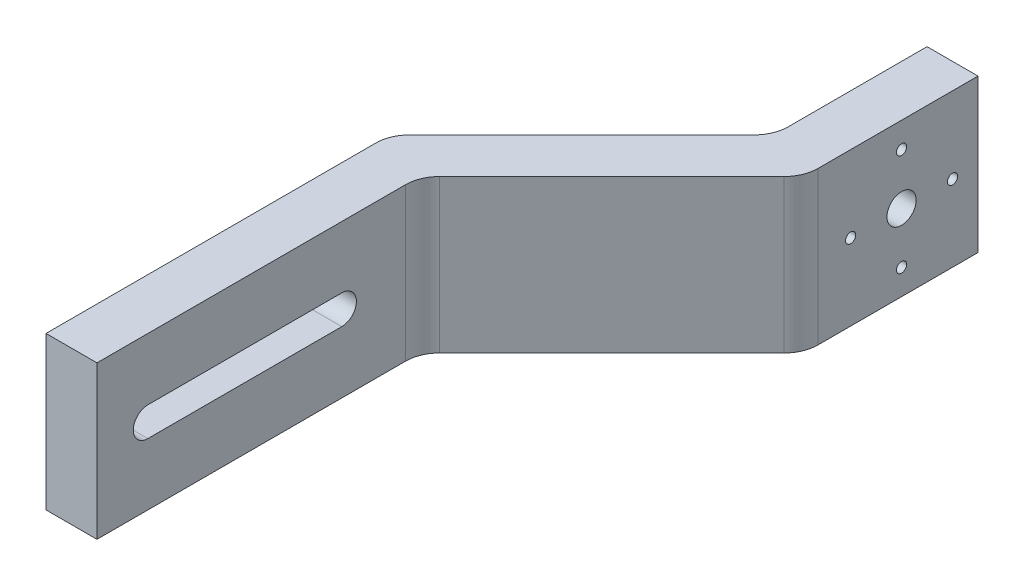
SolidWorks part; units mm, degrees
ref_plane "Front Plane" through (0, 0, 0) normal (0, 0, 1) x (1, 0, 0)
ref_plane "Top Plane" through (0, 0, 0) normal (0, 1, 0) x (1, 0, 0)
ref_plane "Right Plane" through (0, 0, 0) normal (1, 0, 0) x (0, 0, -1)
sketch "Sketch1" plane through (0, 0, 0) normal (0, 1, 0) x (1, 0, 0)
  line L0 (0, 0) -> (0, 101.2132)
  line L1 (0, 101.2132) -> (56.5685, 157.7817)
  line L2 (56.5685, 157.7817) -> (56.5685, 202.7817)
  line L3 (56.5685, 202.7817) -> (71.5685, 202.7817)
  line L4 (71.5685, 202.7817) -> (71.5685, 151.5685)
  line L5 (71.5685, 151.5685) -> (15, 95)
  line L6 (15, 95) -> (15, 0)
  line L7 (15, 0) -> (0, 0)
  dimension "D1" = 15
  dimension "D2" = 15
  dimension "D3" = 15
  dimension "D4" = 80
  dimension "D5" = 45
  dimension "D6" = 95
  dimension "D7" = 135
extrude "Body" add sketch "Sketch1" along normal blind 45
sketch "Sketch3" plane through (56.5685, 0, 0) normal (-1, 0, 0) x (0, 0, 1)
  line L0 (-157.7817, 45) -> (-202.7817, 0) construction
  line L1 (-180.2817, 22.5) -> (-180.2817, 37.5) construction
  circle A0 centre (-180.2817, 22.5) radius 4.3
  circle A1 centre (-180.2817, 22.5) radius 15 construction
  circle A2 centre (-180.2817, 37.5) radius 1.5
  circle A3 centre (-165.2817, 22.5) radius 1.5
  circle A4 centre (-180.2817, 7.5) radius 1.5
  circle A5 centre (-195.2817, 22.5) radius 1.5
  point P9 (-180.2817, 22.5)
  point P10 (-195.2817, 22.5)
  point P18 (-180.2817, 22.5)
  dimension "D1" = 8.6
  dimension "D2" = 30
  dimension "D3" = 3
  dimension "D4" = 4
extrude "Mounting Holes" cut sketch "Sketch3" against normal up to next
sketch "Sketch4" plane through (56.5685, 0, 0) normal (-1, 0, 0) x (0, 0, 1)
  line L0 (-162.4317, 20.8546) -> (-162.4317, 24.1454)
  line L1 (-178.6363, 40.35) -> (-181.9272, 40.35)
  line L2 (-181.9272, 40.35) -> (-183.5726, 37.5)
  line L3 (-183.5726, 37.5) -> (-181.9272, 34.65)
  line L4 (-181.9272, 34.65) -> (-178.6363, 34.65)
  line L5 (-178.6363, 34.65) -> (-176.9908, 37.5)
  line L6 (-176.9908, 37.5) -> (-178.6363, 40.35)
  line L7 (-162.4317, 24.1454) -> (-165.2817, 25.7909)
  line L8 (-165.2817, 25.7909) -> (-168.1317, 24.1454)
  line L9 (-168.1317, 24.1454) -> (-168.1317, 20.8546)
  line L10 (-168.1317, 20.8546) -> (-165.2817, 19.2091)
  line L11 (-165.2817, 19.2091) -> (-162.4317, 20.8546)
  line L12 (-181.9272, 4.65) -> (-178.6363, 4.65)
  line L13 (-178.6363, 4.65) -> (-176.9908, 7.5)
  line L14 (-176.9908, 7.5) -> (-178.6363, 10.35)
  line L15 (-178.6363, 10.35) -> (-181.9272, 10.35)
  line L16 (-181.9272, 10.35) -> (-183.5726, 7.5)
  line L17 (-183.5726, 7.5) -> (-181.9272, 4.65)
  line L18 (-198.1317, 24.1454) -> (-198.1317, 20.8546)
  line L19 (-198.1317, 20.8546) -> (-195.2817, 19.2091)
  line L20 (-195.2817, 19.2091) -> (-192.4317, 20.8546)
  line L21 (-192.4317, 20.8546) -> (-192.4317, 24.1454)
  line L22 (-192.4317, 24.1454) -> (-195.2817, 25.7909)
  line L23 (-195.2817, 25.7909) -> (-198.1317, 24.1454)
  circle A0 centre (-180.2817, 37.5) radius 2.85 construction
  point P1 (-180.2817, 22.5)
  point P30 (-180.2817, 22.5)
  point P31 (-180.2817, 22.5)
  dimension "D1" = 5.7
  dimension "D2" = 4
extrude "Mounting Hole Counterbore" cut sketch "Sketch4" against normal blind 3.5
fillet "Stress Concentration Relief Fillets" radius 10 4 edges at (15, 22.5, -95) (71.5685, 22.5, -151.5685) (0, 22.5, -101.2132) (56.5685, 22.5, -157.7817)
sketch "Sketch5" plane through (0, 0, 0) normal (-1, 0, 0) x (0, 0, 1)
  line L0 (-72.0711, 22.5) -> (-15, 22.5) construction
  line L1 (-72.0711, 26.8) -> (-15, 26.8)
  line L2 (-72.0711, 18.2) -> (-15, 18.2)
  line L3 (-97.0711, 22.5) -> (0, 22.5) construction
  line L4 (0, 45) -> (0, 0) construction
  line L9 (-97.0711, 45) -> (-97.0711, 0) construction
  arc A0 (-72.0711, 26.8) -> (-72.0711, 18.2) centre (-72.0711, 22.5) ccw
  arc A1 (-15, 18.2) -> (-15, 26.8) centre (-15, 22.5) ccw
  point P2 (-43.5355, 22.5)
  point P11 (0, 0)
  dimension "D1" = 4.3
  dimension "D2" = 15
  dimension "D3" = 25
extrude "Slot" cut sketch "Sketch5" against normal through all
